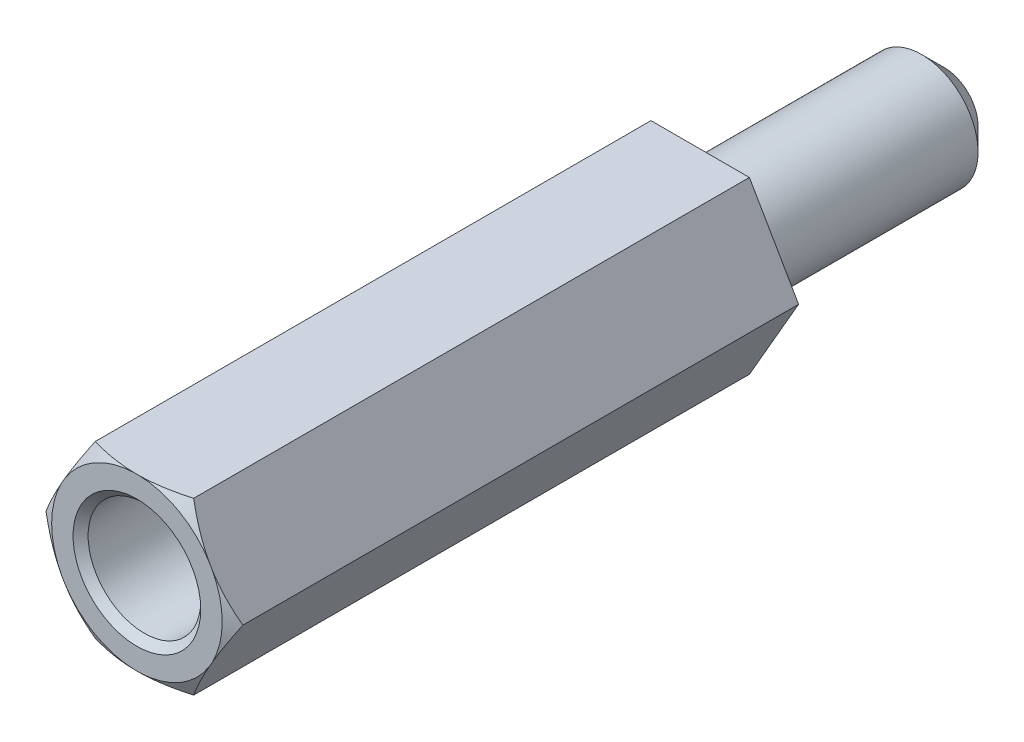
SolidWorks part; units mm, degrees
ref_plane "Front Plane" through (0, 0, 0) normal (0, 0, 1) x (1, 0, 0)
ref_plane "Top Plane" through (0, 0, 0) normal (0, 1, 0) x (1, 0, 0)
ref_plane "Right Plane" through (0, 0, 0) normal (1, 0, 0) x (0, 0, -1)
sketch "Sketch1" plane through (0, 0, 0) normal (0, 0, 1) x (1, 0, 0)
  line L0 (0, 0) -> (2.6212, 0) construction
  line L1 (2.6212, 0) -> (1.3106, 2.27)
  line L2 (1.3106, 2.27) -> (-1.3106, 2.27)
  line L3 (-1.3106, 2.27) -> (-2.6212, 0)
  line L4 (-2.6212, 0) -> (-1.3106, -2.27)
  line L5 (-1.3106, -2.27) -> (1.3106, -2.27)
  line L6 (1.3106, -2.27) -> (2.6212, 0)
  circle A0 centre (0, 0) radius 2.27 construction
  dimension "D1" = 4.54
extrude "Boss-Extrude1" add sketch "Sketch1" along normal blind 15
sketch "Sketch2" plane through (0, 0, 15) normal (0, 0, 1) x (1, 0, 0)
  circle A0 centre (0, 0) radius 1.5
extrude "Cut-Extrude1" cut sketch "Sketch2" against normal blind 12 and the other way through all
sketch "Sketch3" plane through (0, 0, 0) normal (0, 1, 0) x (1, 0, 0)
  line L0 (-2.6212, -15) -> (-2.2712, -15)
  line L1 (-2.2712, -15) -> (-2.6212, -14.8)
  line L2 (-2.6212, -15) -> (-2.6212, 0) construction
  line L3 (-2.6212, -14.8) -> (-2.6212, -15)
  dimension "D1" = 0.35
  dimension "D2" = 0.2
ref_axis "Axis1" through (0, 0, 3) along (0, 0, 1)
revolve "Cut-Revolve1" cut sketch "Sketch3" angle 360 about axis through (0, 0, 3) along (0, 0, 1)
ref_plane "Plane1" through (0, 0, 7.5) normal (0, 0, 1) x (1, 0, 0)
chamfer "Chamfer1" distance 0.2 angle 45 1 edges at (1.5, 0, 15)
sketch "Sketch4" plane through (0, 0, 0) normal (0, 0, -1) x (-1, 0, 0)
  circle A0 centre (0, 0) radius 1.5
extrude "Boss-Extrude2" add sketch "Sketch4" along normal blind 6.5
chamfer "Chamfer2" distance 0.6 angle 45 1 edges at (-1.5, 0, -6.5)
